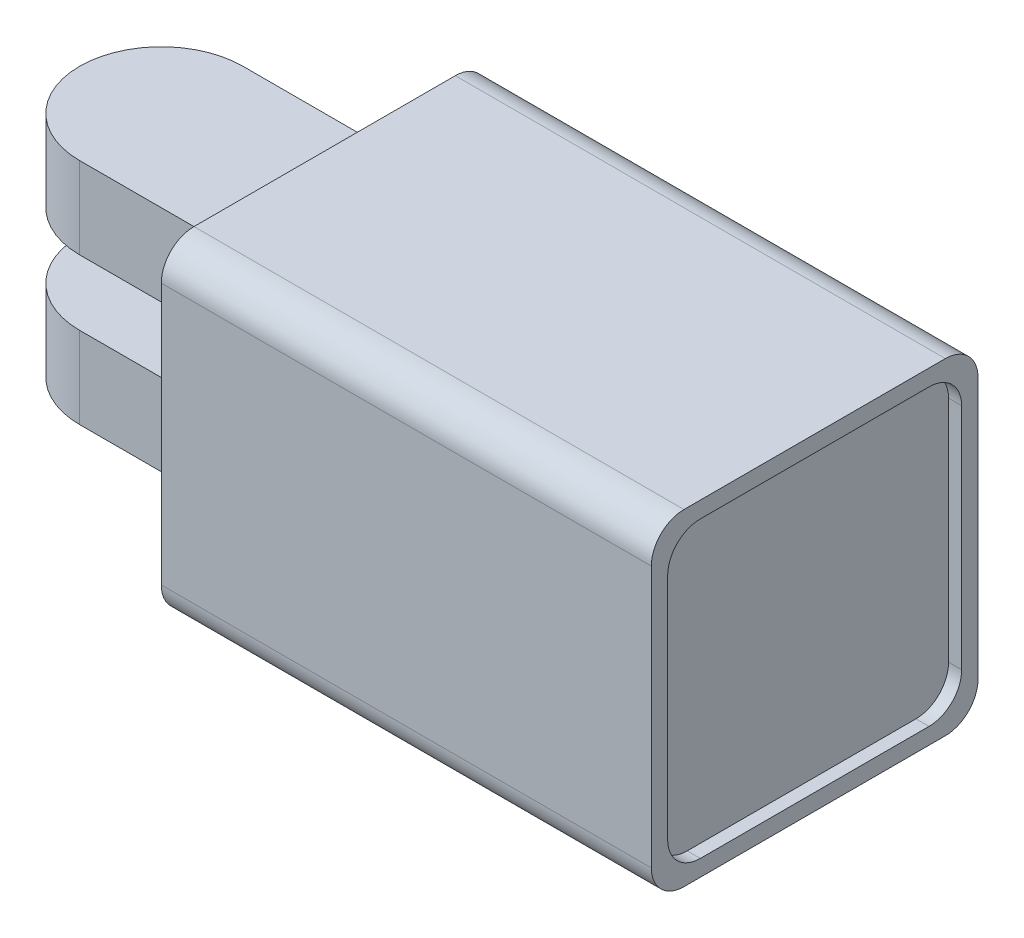
SolidWorks part; units mm, degrees
ref_plane "Front Plane" through (0, 0, 0) normal (0, 0, 1) x (1, 0, 0)
ref_plane "Top Plane" through (0, 0, 0) normal (0, 1, 0) x (1, 0, 0)
ref_plane "Right Plane" through (0, 0, 0) normal (1, 0, 0) x (0, 0, -1)
sketch "Sketch1" plane through (0, 0, 0) normal (0, 1, 0) x (1, 0, 0)
  line L0 (0, 5) -> (10, 5)
  line L1 (10, 5) -> (10, -5)
  line L2 (10, -5) -> (0, -5)
  arc A1 (0, 5) -> (0, -5) centre (0, 0) ccw
  dimension "D2" = 10
extrude "Boss-Extrude1" add sketch "Sketch1" along normal blind 14
sketch "Sketch3" plane through (10, 0, 0) normal (1, 0, 0) x (0, 0, -1)
  line L0 (-5, 0) -> (5, 14) construction
  line L2 (-10, -3) -> (10, -3)
  line L3 (-10, -3) -> (-10, 17)
  line L4 (-10, 17) -> (10, 17)
  line L5 (10, -3) -> (10, 17)
  line L6 (-10, -3) -> (10, 17) construction
  line L7 (-10, 17) -> (10, -3) construction
  point P4 (0, 7)
  dimension "D1" = 20
  dimension "D2" = 20
extrude "Boss-Extrude2" add sketch "Sketch3" along normal blind 30
sketch "Sketch4" plane through (40, 0, 0) normal (1, 0, 0) x (0, 0, -1)
  line L0 (-10, 17) -> (10, -3) construction
  line L1 (-10, 17) -> (-10, -3) construction
  line L3 (-9, 16) -> (9, 16)
  line L4 (-9, 16) -> (-9, -2)
  line L5 (-9, -2) -> (9, -2)
  line L6 (9, 16) -> (9, -2)
  line L7 (-9, 16) -> (9, -2) construction
  line L8 (-9, -2) -> (9, 16) construction
  point P5 (0, 7)
  dimension "D1" = 18
extrude "Cut-Extrude1" cut sketch "Sketch4" against normal blind 3
sketch "Sketch5" plane through (37, 0, 0) normal (1, 0, 0) x (0, 0, -1)
  line L0 (-9, 16) -> (9, -2)
  line L6 (-4, 11) -> (4, 3) construction
  circle A0 centre (0, 7) radius 4
  point P4 (0, 7)
  dimension "D1" = 8
fillet "Fillet2" radius 2 4 edges at (25, 17, -10) (25, -3, -10) (25, -3, 10) (25, 17, 10)
fillet "Fillet3" radius 2 4 edges at (38.5, 16, -9) (38.5, -2, -9) (38.5, -2, 9) (38.5, 16, 9)
extrude "Cut-Extrude2" cut sketch "Sketch5" against normal blind 0.5 contours L0 A0 | L0 A0
ref_plane "Plane1" through (39, 0, 0) normal (1, 0, 0) x (0, 0, -1)
sketch "Sketch6" plane through (39, 0, 0) normal (1, 0, 0) x (0, 0, -1)
  line L1 (-7, 16) -> (7, 16)
  line L2 (-9, 14) -> (-9, 0)
  line L3 (-7, -2) -> (7, -2)
  line L4 (9, 14) -> (9, 0)
  arc A0 (-9, 14) -> (-7, 16) centre (-7, 14) cw
  arc A1 (7, 16) -> (9, 14) centre (7, 14) cw
  arc A2 (9, 0) -> (7, -2) centre (7, 0) cw
  arc A3 (-7, -2) -> (-9, 0) centre (-7, 0) cw
  point P0 (0, 7)
extrude "Boss-Extrude3" add sketch "Sketch6" along normal blind 0.2
sketch "Sketch8" plane through (0, 0, -5) normal (0, 0, -1) x (-1, 0, 0)
  line L0 (0, 14) -> (0, 9.0277) construction
  line L7 (0, 4.1729) -> (0, 0) construction
  line L8 (0, 14) -> (0, 0) construction
  line L9 (-5, 9) -> (5, 9)
  line L10 (-5, 9) -> (-5, 5)
  line L11 (-5, 5) -> (5, 5)
  line L12 (5, 9) -> (5, 5)
  line L13 (-5, 9) -> (5, 5) construction
  line L14 (-5, 5) -> (5, 9) construction
  line L15 (5, 0) -> (5, 14) construction
  point P4 (0, 7)
  dimension "D1" = 4
extrude "Cut-Extrude4" cut sketch "Sketch8" against normal blind 20
